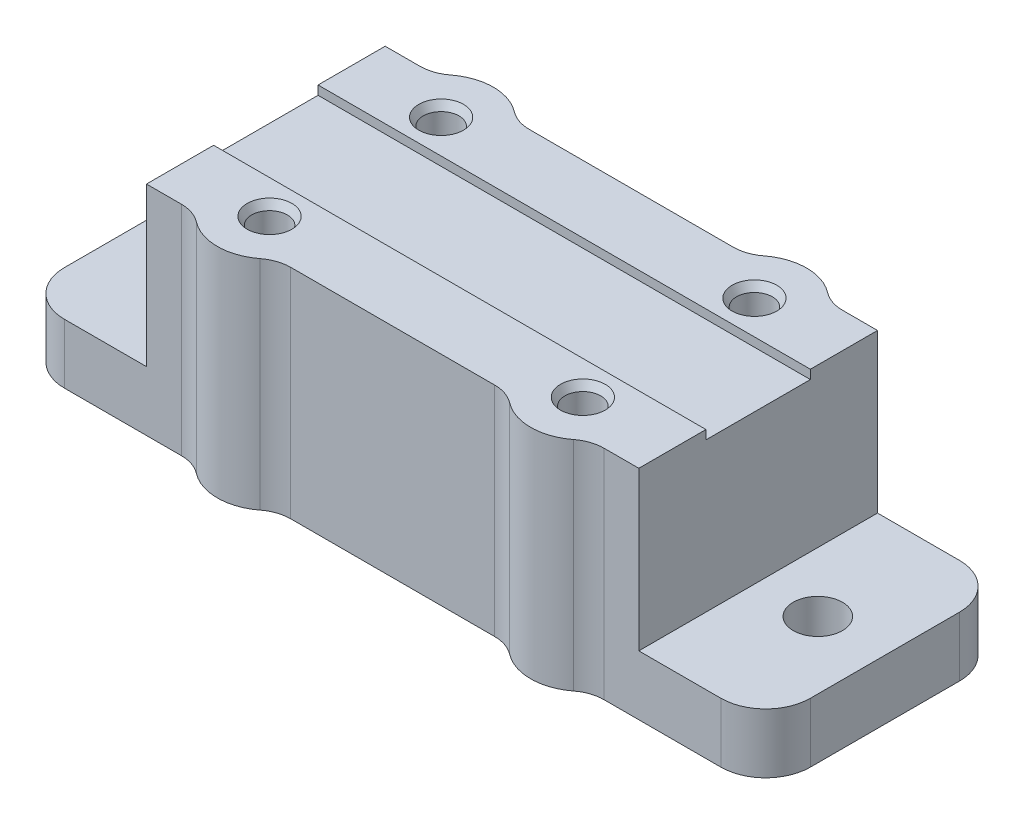
SolidWorks part; units mm, degrees
ref_plane "Alzado" through (0, 0, 0) normal (0, 0, 1) x (1, 0, 0)
ref_plane "Planta" through (0, 0, 0) normal (0, 1, 0) x (1, 0, 0)
ref_plane "Vista lateral" through (0, 0, 0) normal (1, 0, 0) x (0, 0, -1)
sketch "Croquis1" plane through (0, 0, 0) normal (0, 1, 0) x (1, 0, 0)
  line L0 (25, 0) -> (25, -16) construction
  line L1 (0, 0) -> (50, 0)
  line L2 (0, 0) -> (0, -16)
  line L3 (0, -16) -> (50, -16)
  line L4 (50, 0) -> (50, -16)
  line L5 (25, -8) -> (0, -8) construction
  circle A0 centre (4.5, -8) radius 1.65
  circle A1 centre (45.5, -8) radius 1.65
  dimension "D3" = 3.3
  dimension "D4" = 20.5
  dimension "D1" = 50
  dimension "D2" = 16
extrude "Saliente-Extruir1" add sketch "Croquis1" along normal blind 4
sketch "Croquis2" plane through (0, 4, 0) normal (0, 1, 0) x (1, 0, 0)
  line L0 (25, 0) -> (25, -16) construction
  line L1 (50, 0) -> (0, 0) construction
  line L2 (0, -16) -> (50, -16) construction
  line L3 (8.5, 0) -> (8.5, -16)
  line L4 (8.5, -16) -> (41.5, -16)
  line L5 (8.5, 0) -> (41.5, 0)
  line L6 (0, 0) -> (0, -16) construction
  line L7 (41.5, 0) -> (41.5, -16)
  dimension "D1" = 8.5
extrude "Saliente-Extruir2" add sketch "Croquis2" along normal blind 10
sketch "Croquis3" plane through (0, 14, 0) normal (0, 1, 0) x (1, 0, 0)
  line L0 (8.5, -8) -> (41.5, -8) construction
  line L1 (8.5, 0) -> (8.5, -16) construction
  line L2 (41.5, -16) -> (41.5, 0) construction
  line L3 (41.5, 0) -> (41.5, -4.5)
  line L4 (8.5, -16) -> (41.5, -16)
  line L5 (8.5, -16) -> (8.5, -11.5)
  line L6 (8.5, -11.5) -> (41.5, -11.5)
  line L7 (41.5, -16) -> (41.5, -11.5)
  line L8 (8.5, 0) -> (41.5, 0)
  line L9 (8.5, 0) -> (8.5, -4.5)
  line L10 (8.5, -4.5) -> (41.5, -4.5)
  dimension "D1" = 3.5
extrude "Saliente-Extruir3" add sketch "Croquis3" along normal blind 0.6
sketch "Croquis4" plane through (0, 14.6, 0) normal (0, 1, 0) x (1, 0, 0)
  line L0 (25, -16) -> (25, 0) construction
  line L1 (8.5, -16) -> (41.5, -16) construction
  line L2 (41.5, 0) -> (8.5, 0) construction
  line L4 (14.5, -16) -> (14.5, 0) construction
  line L7 (8.5, -11.5) -> (8.5, -16) construction
  line L9 (14.5, -8) -> (25, -8) construction
  line L10 (8.5, -13.75) -> (14.5, -13.75) construction
  circle A0 centre (14.5, -13.75) radius 1.2
  circle A1 centre (14.5, -2.25) radius 1.2
  circle A2 centre (35.5, -13.75) radius 1.2
  circle A3 centre (35.5, -2.25) radius 1.2
  dimension "D2" = 2.4
  dimension "D1" = 6
extrude "Cortar-Extruir1" cut sketch "Croquis4" against normal blind 8
sketch "Croquis5" plane through (0, 14.6, 0) normal (0, 1, 0) x (1, 0, 0)
  line L0 (18.1657, -16) -> (10.8343, -16)
  line L3 (14.5, -17.25) -> (14.5, -13.75) construction
  arc A0 (12.3617, -16.5208) -> (16.6383, -16.5208) centre (14.5, -13.75) ccw
  arc A1 (12.3617, -16.5208) -> (10.8343, -16) centre (10.8343, -18.5) ccw
  arc A2 (16.6383, -16.5208) -> (18.1657, -16) centre (18.1657, -18.5) cw
  dimension "D1" = 7
  dimension "D2" = 5
extrude "Saliente-Extruir5" add sketch "Croquis5" against normal up to vertex (14.6 mm away)
ref_plane "Plano1" through (0, 0, 8) normal (0, 0, 1) x (1, 0, 0)
ref_plane "Plano2" through (25, 0, 0) normal (-1, 0, 0) x (0, 0, 1)
mirror "Simetría1" about plane through (25, 0, 0) normal (-1, 0, 0) of "Saliente-Extruir5"
mirror "Simetría2" about plane through (0, 0, 8) normal (0, 0, 1) of "Simetría1", "Saliente-Extruir5"
fillet "Redondeo1" radius 3 2 edges at (0, 2, 16)
fillet "Redondeo2" radius 3 1 edges at (0, 2, 0)
fillet "Redondeo3" radius 3 2 edges at (50, 2, 0)
fillet "Redondeo4" radius 3 1 edges at (50, 2, 16)
sketch "Croquis6" plane through (0, 14.6, 0) normal (0, 1, 0) x (1, 0, 0)
  circle A0 centre (14.5, -13.75) radius 1.5
  dimension "D1" = 3
extrude "Cortar-Extruir2" cut sketch "Croquis6" against normal blind 0.6 draft 30
mirror "Simetría5" about plane through (25, 0, 0) normal (-1, 0, 0) of "Cortar-Extruir2"
mirror "Simetría6" about plane through (0, 0, 8) normal (0, 0, 1) of "Simetría5", "Cortar-Extruir2"
